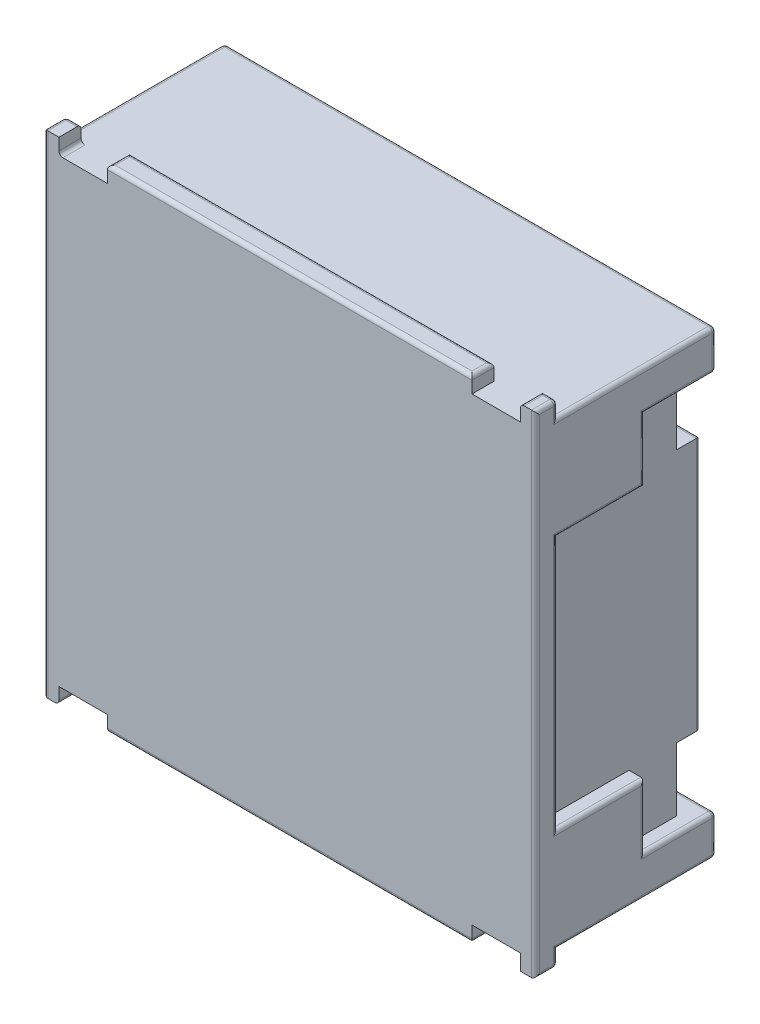
SolidWorks part; units mm, degrees
material "CA"
ref_plane "Front Plane" through (0, 0, 0) normal (0, 0, 1) x (1, 0, 0)
ref_plane "Top Plane" through (0, 0, 0) normal (0, 1, 0) x (1, 0, 0)
ref_plane "Right Plane" through (0, 0, 0) normal (1, 0, 0) x (0, 0, -1)
sketch "Sketch1" plane through (0, 0, 0) normal (0, 0, 1) x (1, 0, 0)
  line L0 (0, 0) -> (0, 4329.0416) construction
  line L1 (-3.1, 3.1) -> (3.1, 3.1)
  line L2 (-3.1, 3.1) -> (-3.1, -3.1)
  line L3 (-3.1, -3.1) -> (3.1, -3.1)
  line L4 (3.1, 3.1) -> (3.1, -3.1)
  line L5 (0, 0) -> (4329.0416, 0) construction
  dimension "D1" = 6.2
extrude "Boss-Extrude1" add sketch "Sketch1" along normal blind 2.38
sketch "Sketch2" plane through (0, 0, 0) normal (0, 0, -1) x (-1, 0, 0)
  line L0 (0, 0) -> (0, 50000) construction
  line L1 (0, 0) -> (50000, 0) construction
  line L2 (-3.1, -3.1) -> (-3.1, 3.1) construction
  line L3 (-3.1, 2.4) -> (-1.1, 2.4)
  line L4 (-3.1, 2.4) -> (-3.1, 1.6)
  line L5 (-3.1, 1.6) -> (-1.1, 1.6)
  line L6 (-1.1, 2.4) -> (-1.1, 1.6)
  line L7 (-1.1, 2) -> (49998.9, 2) construction
  line L8 (1.1, 2.4) -> (1.1, 1.6)
  line L9 (3.1, 2.4) -> (1.1, 2.4)
  line L10 (3.1, 1.6) -> (1.1, 1.6)
  line L11 (3.1, 2.4) -> (3.1, 1.6)
  line L12 (3.1, -2.4) -> (3.1, -1.6)
  line L13 (3.1, -2.4) -> (1.1, -2.4)
  line L14 (3.1, -1.6) -> (1.1, -1.6)
  line L15 (1.1, -2.4) -> (1.1, -1.6)
  line L16 (-1.1, -2.4) -> (-1.1, -1.6)
  line L17 (-3.1, -2.4) -> (-1.1, -2.4)
  line L18 (-3.1, -2.4) -> (-3.1, -1.6)
  line L19 (-3.1, -1.6) -> (-1.1, -1.6)
  point P13 (-1.1, 2)
  dimension "D1" = 0.8
  dimension "D2" = 2
  dimension "D3" = 2
extrude "Cut-Extrude1" cut sketch "Sketch2" against normal blind 0.4
sketch "Sketch3" plane through (0, 3.1, 0) normal (0, 1, 0) x (1, 0, 0)
  line L0 (3.1, -2.38) -> (3.1, 0) construction
  line L1 (-3.1, 0) -> (3.1, 0)
  line L2 (-3.1, 0) -> (-3.1, -0.1)
  line L3 (-3.1, -0.1) -> (3.1, -0.1)
  line L4 (3.1, 0) -> (3.1, -0.1)
  dimension "D1" = 0.1
extrude "Cut-Extrude2" cut sketch "Sketch3" against normal through all
sketch "Sketch14" plane through (0, 0, 0.1) normal (0, 0, -1) x (-1, 0, 0)
  line L0 (1.1, 1.6) -> (3.1, 1.6) construction
  line L1 (3.1, -1.6) -> (2.9, -1.6)
  line L2 (3.1, -1.6) -> (3.1, 1.6)
  line L3 (3.1, 1.6) -> (2.9, 1.6)
  line L4 (2.9, -1.6) -> (2.9, 1.6)
  line L5 (-3.1, 1.6) -> (-1.1, 1.6) construction
  line L6 (-3.1, -1.6) -> (-2.9, -1.6)
  line L7 (-3.1, -1.6) -> (-3.1, 1.6)
  line L8 (-3.1, 1.6) -> (-2.9, 1.6)
  line L9 (-2.9, -1.6) -> (-2.9, 1.6)
  line L10 (0, 0) -> (0, -50000) construction
  dimension "D1" = 0.2
extrude "Cut-Extrude3" cut sketch "Sketch14" against normal blind 2
sketch "Sketch16" plane through (-3.1, 0, 0) normal (-1, 0, 0) x (0, 0, 1)
  line L0 (0, 0) -> (50000, 0) construction
  line L1 (0.1, -3.1) -> (2.1, -3.1)
  line L2 (0.1, -3.1) -> (0.1, -2.9)
  line L3 (0.1, -2.9) -> (2.1, -2.9)
  line L4 (2.1, -3.1) -> (2.1, -2.9)
  line L5 (2.1, 3.1) -> (2.1, 2.9)
  line L6 (0.1, 3.1) -> (2.1, 3.1)
  line L7 (0.1, 2.9) -> (2.1, 2.9)
  line L8 (0.1, 3.1) -> (0.1, 2.9)
  dimension "D1" = 0.2
extrude "Cut-Extrude4" cut sketch "Sketch16" against normal through all
sketch "Sketch19" plane through (0, 0, 2.1) normal (0, 0, -1) x (-1, 0, 0)
  line L0 (-3.1, -2.9) -> (3.1, -2.9) construction
  line L1 (-2.91, -2.9) -> (-2.3, -2.9)
  line L2 (-2.91, -2.9) -> (-2.91, -3.1)
  line L3 (-2.91, -3.1) -> (-2.3, -3.1)
  line L4 (-2.3, -2.9) -> (-2.3, -3.1)
  line L5 (-3.1, -3.1) -> (3.1, -3.1) construction
  line L6 (0, 0) -> (0, -50000) construction
  line L7 (0, 0) -> (50000, 0) construction
  line L8 (2.91, -3.1) -> (2.3, -3.1)
  line L9 (2.91, -2.9) -> (2.3, -2.9)
  line L10 (2.91, -2.9) -> (2.91, -3.1)
  line L11 (2.3, -2.9) -> (2.3, -3.1)
  line L12 (0, 0) -> (-50000, 0) construction
  line L13 (2.91, 3.1) -> (2.3, 3.1)
  line L14 (2.91, 2.9) -> (2.91, 3.1)
  line L15 (2.91, 2.9) -> (2.3, 2.9)
  line L16 (2.3, 2.9) -> (2.3, 3.1)
  line L17 (-2.91, 3.1) -> (-2.3, 3.1)
  line L18 (-2.3, 2.9) -> (-2.3, 3.1)
  line L19 (-2.91, 2.9) -> (-2.3, 2.9)
  line L20 (-2.91, 2.9) -> (-2.91, 3.1)
  dimension "D1" = 2.3
  dimension "D2" = 2.91
extrude "Cut-Extrude5" cut sketch "Sketch19" against normal through all
sketch "Sketch20" plane through (0, 0, 0.4) normal (0, 0, -1) x (-1, 0, 0)
  line L2 (-2.9, -1.6) -> (-3.1, -1.6)
  line L3 (-2.9, -1.6) -> (-2.9, -2.4)
  line L4 (-2.9, -2.4) -> (-3.1, -2.4)
  line L5 (-3.1, -1.6) -> (-3.1, -2.4)
  line L6 (-3.1, 2.4) -> (-2.9, 2.4)
  line L7 (-3.1, 2.4) -> (-3.1, 1.6)
  line L8 (-3.1, 1.6) -> (-2.9, 1.6)
  line L9 (-2.9, 2.4) -> (-2.9, 1.6)
  line L10 (2.9, 1.6) -> (3.1, 1.6)
  line L11 (2.9, 1.6) -> (2.9, 2.4)
  line L12 (2.9, 2.4) -> (3.1, 2.4)
  line L13 (3.1, 1.6) -> (3.1, 2.4)
  line L14 (2.9, -1.6) -> (3.1, -1.6)
  line L15 (2.9, -1.6) -> (2.9, -2.4)
  line L16 (2.9, -2.4) -> (3.1, -2.4)
  line L17 (3.1, -1.6) -> (3.1, -2.4)
extrude "Cut-Extrude6" cut sketch "Sketch20" against normal blind 0.6
fillet "Fillet1" radius 0.05 63 edges at (2.3, -3.1, 2.24) (0, -3.1, 2.1) (-2.3, -3.1, 2.24) (0, -3.1, 2.38) (-2.3, 3.1, 2.24) (0, 3.1, 2.1) (2.3, 3.1, 2.24) (0, 3.1, 2.38) (-3.1, -1.6, 1.55) (-3.1, 0, 2.1) (-3.1, 1.6, 1.55) (-3.1, 2, 1) (-3.1, 2.4, 0.55) (-3.1, 2.9, 1.1) (-3.1, 3, 2.1) (-3.1, 3.1, 2.24) (-3.1, 0, 2.38) (-3.1, -3.1, 2.24) (-3.1, -3, 2.1) (-3.1, -2.9, 1.1) (-3.1, -2.4, 0.55) (-3.1, -2, 1) (-2.1, 2.4, 0.1) (-1.1, 2, 0.1) (-2, 1.6, 0.1) (-2.9, 0, 0.1) (-2, -1.6, 0.1) (-1.1, -2, 0.1) (-2.1, -2.4, 0.1) (-3.1, -2.65, 0.1) (0, -2.9, 0.1) (2.1, -2.4, 0.1) (1.1, -2, 0.1) (2, -1.6, 0.1) (2.9, 0, 0.1) (2, 1.6, 0.1) (1.1, 2, 0.1) (2.1, 2.4, 0.1) (0, 2.9, 0.1) (-3.1, 2.65, 0.1) (3.1, 1.6, 1.55) (3.1, 0, 2.1) (3.1, -1.6, 1.55) (3.1, -2, 1) (3.1, -2.4, 0.55) (3.1, -2.65, 0.1) (3.1, -2.9, 1.1) (3.1, -3, 2.1) (3.1, -3.1, 2.24) (3.1, 0, 2.38) (3.1, 3.1, 2.24) (3.1, 3, 2.1) (3.1, 2.9, 1.1) (3.1, 2.65, 0.1) (3.1, 2.4, 0.55) (3.1, 2, 1) (3.005, -3.1, 2.1) (-2.91, -3.1, 2.24) (-2.91, -3, 2.1) (3.005, 3.1, 2.1) (2.91, 3.1, 2.24) (-3.005, 3.1, 2.1) (-2.91, 2.9, 2.24)
